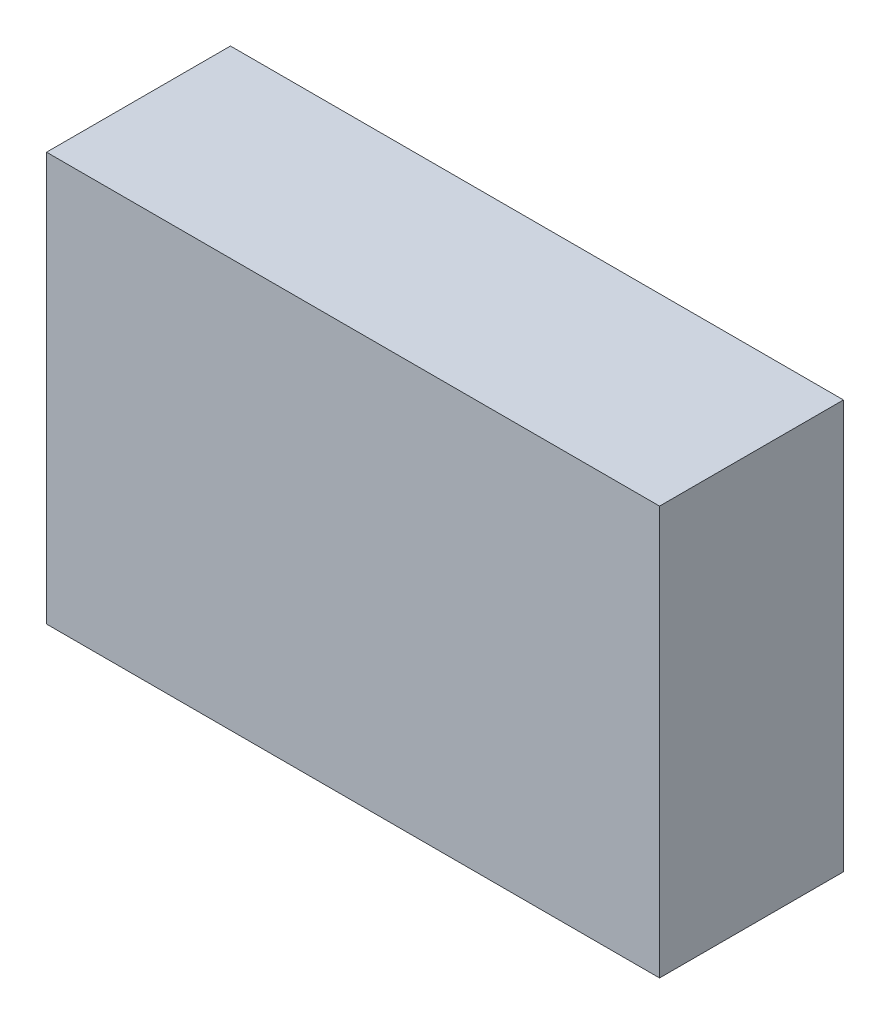
SolidWorks part; units mm, degrees
ref_plane "Front Plane" through (0, 0, 0) normal (0, 0, 1) x (1, 0, 0)
ref_plane "Top Plane" through (0, 0, 0) normal (0, 1, 0) x (1, 0, 0)
ref_plane "Right Plane" through (0, 0, 0) normal (1, 0, 0) x (0, 0, -1)
sketch "Sketch1" plane through (0, 0, 0) normal (0, 1, 0) x (1, 0, 0)
  line L1 (0, 0) -> (150, 0)
  line L2 (0, 0) -> (0, 45)
  line L3 (0, 45) -> (150, 45)
  line L4 (150, 0) -> (150, 45)
  dimension "D1" = 45
  dimension "D2" = 150
extrude "Boss-Extrude1" add sketch "Sketch1" along normal blind 100
